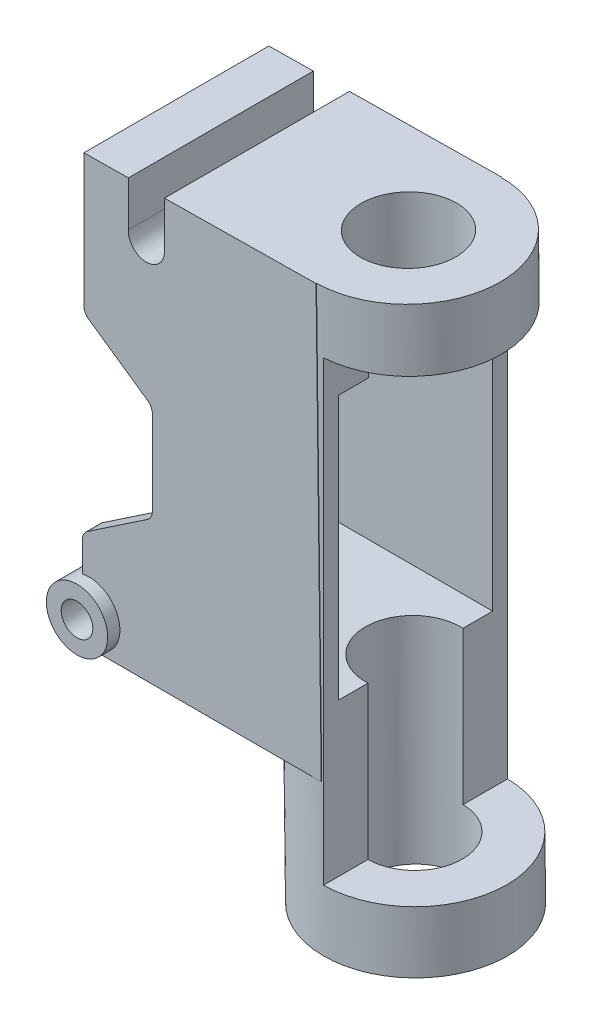
SolidWorks part; units mm, degrees
ref_plane "Front Plane" through (0, 0, 0) normal (0, 0, 1) x (1, 0, 0)
ref_plane "Top Plane" through (0, 0, 0) normal (0, 1, 0) x (1, 0, 0)
ref_plane "Right Plane" through (0, 0, 0) normal (1, 0, 0) x (0, 0, -1)
sketch "Sketch2" plane through (0, 0, 0) normal (0, 0, 1) x (1, 0, 0)
  line L0 (-622.8966, 615.8381) -> (-568.9394, 614.4505) construction
  line L1 (-1.7546, 128.969) -> (-1.7546, 83.8238)
  line L2 (-1.7546, 83.8238) -> (20.5921, 68.3166)
  line L3 (20.5921, 68.3166) -> (20.5921, 36.8461)
  line L4 (20.5921, 36.8461) -> (-2.2524, 21.476)
  line L5 (-2.2524, 21.476) -> (-2.2524, 12.415)
  line L6 (-1.7546, 128.969) -> (12.7656, 129.1466)
  line L7 (73.9604, 129.8951) -> (75.6491, -8.1618)
  line L8 (75.6491, -8.1618) -> (-2.2524, -8.1618)
  line L9 (-2.2524, -8.1618) -> (-2.2524, 12.415)
  line L10 (24.5303, 129.2905) -> (24.5303, 114.1486)
  line L11 (12.7656, 129.1466) -> (12.7656, 113.7814)
  line L12 (24.5303, 129.2905) -> (73.9604, 129.8951)
  arc A0 (12.7656, 114.5159) -> (24.5303, 114.1486) centre (18.6422, 114.1486) ccw
  dimension "D1" = 53.975
extrude "Boss-Extrude1" add sketch "Sketch2" along normal blind 60.325 contours A0 L11 L6 L1 L2 L3 L4 L5 L9 L8 L7 L12 L10
sketch "Sketch4" plane through (0, 0, 60.325) normal (0, 0, 1) x (1, 0, 0)
  circle A0 centre (0, 0) radius 10
  dimension "D1" = 20
extrude "Boss-Extrude2" add sketch "Sketch4" against normal offset from surface (68.325 mm away) 4 from offset 4
sketch "Sketch5" plane through (0, 0, 64.325) normal (0, 0, 1) x (1, 0, 0)
  circle A0 centre (0, 0) radius 5.1594
  dimension "D1" = 10.3187
extrude "Cut-Extrude1" cut sketch "Sketch5" against normal through all
sketch "Sketch6" plane through (0, -8.1618, 0) normal (0, -1, 0) x (1, 0, 0)
  line L0 (75.6491, 0) -> (0, 0)
  line L1 (0, 0) -> (0, 60.325)
  line L2 (0, 60.325) -> (75.6491, 60.325)
  line L3 (75.6491, 60.325) -> (75.6491, 0) construction
  line L4 (75.6491, 60.325) -> (5.778, 60.325) construction
  line L5 (75.6491, 60.325) -> (75.6491, 0)
extrude "Boss-Extrude3" add sketch "Sketch6" along normal blind 1.8288
sketch "Sketch8" plane through (-1.5776, 128.9711, 0) normal (-0.0122, 0.9999, 0) x (0.9999, 0.0122, 0)
  line L0 (75.5436, -60.325) -> (75.5436, 0) construction
  circle A0 centre (75.5436, -30.1625) radius 30
  dimension "D1" = 60
extrude "Boss-Extrude4" add sketch "Sketch8" against normal offset from surface (188.5329 mm away) 49
sketch "Sketch9" plane through (-1.5776, 128.9711, 0) normal (-0.0122, 0.9999, 0) x (0.9999, 0.0122, 0)
  circle A0 centre (75.5436, -30.1625) radius 15.5
  dimension "D1" = 31
extrude "Cut-Extrude2" cut sketch "Sketch9" against normal through all
ref_plane "Plane1" through (125.2454, 0, 0) normal (-1, 0, 0) x (0, 0, 1)
sketch "Sketch10" plane through (125.2454, 0, 0) normal (-1, 0, 0) x (0, 0, 1)
  line L0 (60.325, 109.9147) -> (60.1625, -38.9906)
  line L1 (60.325, 129.8951) -> (60.325, -8.1618) construction
  line L2 (60.1625, -58.9906) -> (60.1625, -8.1618) construction
  line L3 (60.1625, -38.9906) -> (-4.1231, -38.9906)
  line L4 (-4.1231, -38.9906) -> (-4.1231, 109.9147)
  line L5 (-4.1231, 109.9147) -> (60.325, 109.9147)
  line L6 (0.1625, -58.9906) -> (60.1625, -58.9906) construction
  dimension "D1" = 20
extrude "Cut-Extrude3" cut sketch "Sketch10" along normal blind 49
sketch "Sketch11" plane through (-2.2524, 0, 0) normal (-1, 0, 0) x (0, 0, 1)
  line L0 (55.325, 10.8258) -> (5, 10.8258)
  line L1 (5, 10.8258) -> (5, 96.969)
  line L2 (5, 96.969) -> (55.325, 96.969)
  line L3 (55.325, 96.969) -> (55.325, 10.8258)
  line L4 (60.325, 68.3166) -> (60.325, 36.8461) construction
  line L5 (0, 68.3166) -> (0, 36.8461) construction
  line L6 (60.325, 128.969) -> (0, 128.969) construction
  dimension "D1" = 5
  dimension "D2" = 5
  dimension "D3" = 32
extrude "Cut-Extrude4" cut sketch "Sketch11" against normal through all
sketch "Sketch15" plane through (-1.5776, 128.9711, 0) normal (-0.0122, 0.9999, 0) x (0.9999, 0.0122, 0)
  line L0 (14.3443, -30.1625) -> (26.1098, -30.1625) construction
  line L1 (14.3443, -60.325) -> (14.3443, 0) construction
  line L2 (26.1098, -60.325) -> (26.1098, 0) construction
  circle A0 centre (20.227, -30.1625) radius 3.175
  dimension "D1" = 6.35
extrude "Cut-Extrude5" cut sketch "Sketch15" against normal through all
fillet "Fillet1" radius 3.81 8 edges at (-1.7546, 83.8238, 2.5) (20.5921, 36.8461, 2.5) (20.5921, 68.3166, 2.5) (-2.2524, 21.476, 2.5) (-2.2524, 21.476, 57.825) (20.5921, 36.8461, 57.825) (20.5921, 68.3166, 57.825) (-1.7546, 83.8238, 57.825)
